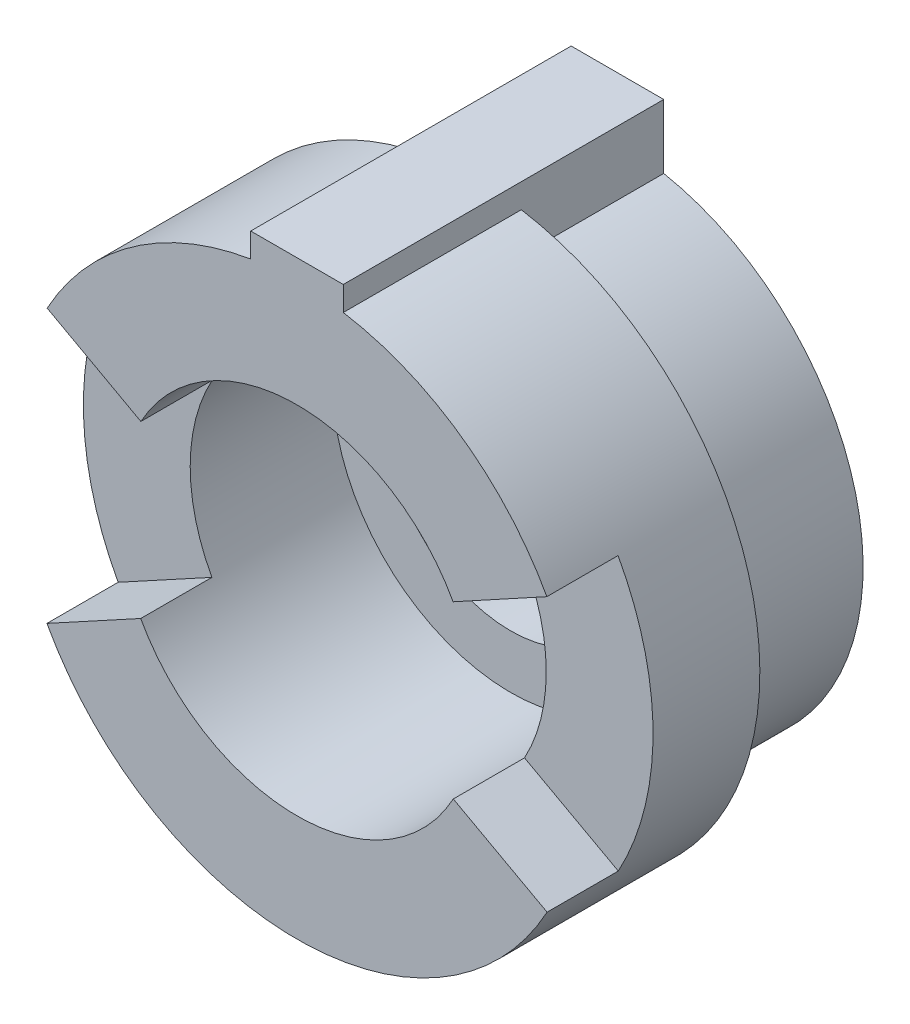
SolidWorks part; units mm, degrees
ref_plane "Front Plane" through (0, 0, 0) normal (0, 0, 1) x (1, 0, 0)
ref_plane "Top Plane" through (0, 0, 0) normal (0, 1, 0) x (1, 0, 0)
ref_plane "Right Plane" through (0, 0, 0) normal (1, 0, 0) x (0, 0, -1)
sketch "Sketch1" plane through (0, 0, 0) normal (0, 0, 1) x (1, 0, 0)
  circle A0 centre (0, 0) radius 8
  circle A1 centre (0, 0) radius 3.5
  dimension "D1" = 7
  dimension "D2" = 16
extrude "Boss-Extrude1" add sketch "Sketch1" along normal blind 3
sketch "Sketch2" plane through (0, 0, 3) normal (0, 0, 1) x (1, 0, 0)
  circle A0 centre (0, 0) radius 8
  circle A1 centre (0, 0) radius 5
  dimension "D1" = 16
  dimension "D2" = 10
extrude "Boss-Extrude2" add sketch "Sketch2" along normal blind 6
sketch "Sketch4" plane through (0, 0, 0) normal (0, 1, 0) x (1, 0, 0)
  line L0 (-8.56, -9) -> (-8.56, -7)
  line L1 (-16.56, -9) -> (-8.56, -9)
  line L2 (8.56, -9) -> (8.56, -7)
  line L3 (8.56, -9) -> (16.56, -9)
  line L4 (-16.56, -9) -> (-16.56, -7)
  line L5 (-16.56, -7) -> (-8.56, -7)
  line L6 (16.56, -9) -> (16.56, -7)
  line L7 (16.56, -7) -> (8.56, -7)
  dimension "D1" = 7
  dimension "D2" = 8.56
  dimension "D3" = 2
  dimension "D4" = 8.56
  dimension "D5" = 8
  dimension "D6" = 8
  dimension "D7" = 2
  dimension "D8" = 7
wrap "Wrap3" sketch "Sketch4" wrap type deboss source sketch "Sketch4" thickness 4 face at (8, 0, 0) parameters "D1"=4
sketch "Sketch5" plane through (0, 0, 0) normal (0, 0, -1) x (-1, 0, 0)
  line L0 (-1.3, 6.7764) -> (-1.3, 7.8937)
  line L2 (1.3, 7.8937) -> (1.3, 6.7764)
  arc A0 (-1.3, 7.8937) -> (1.3, 7.8937) centre (0, 0) ccw
  arc A1 (-1.3, 6.7764) -> (1.3, 6.7764) centre (0, 0) ccw
  circle A2 centre (0, 0) radius 8 construction
  dimension "D1" = 8
  dimension "D3" = 6.9
  dimension "D2" = 1.3
extrude "Cut-Extrude1" cut sketch "Sketch5" against normal blind 4
sketch "Sketch6" plane through (0, 0, 0) normal (0, 0, -1) x (-1, 0, 0)
  line L0 (-1.3, 7.7971) -> (-1.3, 8.5764)
  line L1 (-1.3, 8.5764) -> (1.3, 8.5764)
  line L2 (1.3, 8.5764) -> (1.3, 7.7971)
  line L3 (-1.3, 6.7764) -> (-1.3, 7.8937) construction
  arc A0 (1.3, 7.7971) -> (-1.3, 7.7971) centre (0, -0.0965) ccw
  dimension "D1" = 8
  dimension "D2" = 1.3
  dimension "D3" = 1.0207
  dimension "D4" = 1.8
extrude "Boss-Extrude3" add sketch "Sketch6" against normal blind 9
equation "\"D3@Sketch5\"= 7 - \"tol1@parametersSketch@prostheticParameters.SLDPRT\" / 2"
equation "\"D2@Sketch5\"= 1.5 - \"tol2@parametersSketch@prostheticParameters.SLDPRT\""
equation "\"D2@Sketch6\"= 1.5 - \"tol2@parametersSketch@prostheticParameters.SLDPRT\""
equation "\"D4@Sketch6\"= 2 - \"tol2@parametersSketch@prostheticParameters.SLDPRT\""
